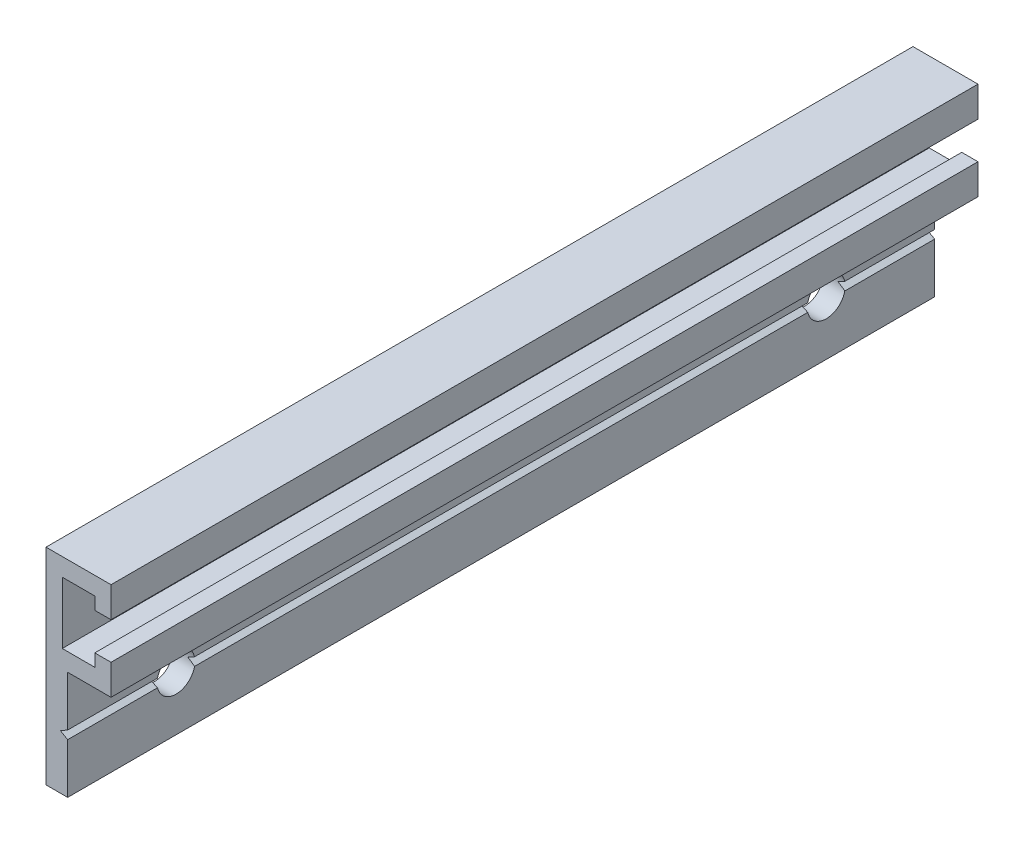
SolidWorks part; units mm, degrees
ref_plane "Front" through (0, 0, 0) normal (0, 0, 1) x (1, 0, 0)
ref_plane "Top" through (0, 0, 0) normal (0, 1, 0) x (1, 0, 0)
ref_plane "Right" through (0, 0, 0) normal (1, 0, 0) x (0, 0, -1)
sketch "Sketch1" plane through (0, 0, 0) normal (0, 0, 1) x (1, 0, 0)
  line L0 (6, -2.8) -> (6, 0)
  line L1 (6, 0) -> (0, 0)
  line L2 (0, 0) -> (0, -19)
  line L3 (0, -19) -> (2, -19)
  line L4 (2, -19) -> (2, -14.3845)
  line L5 (2, -14.3845) -> (1.334, -14)
  line L6 (1.334, -14) -> (2, -13.6155)
  line L7 (2, -13.6155) -> (2, -9)
  line L8 (2, -9) -> (6, -9)
  line L9 (6, -9) -> (6, -6.2)
  line L10 (6, -6.2) -> (4.5, -6.2)
  line L11 (4.5, -6.2) -> (4.5, -7.35)
  line L12 (4.5, -7.35) -> (1.5, -7.35)
  line L13 (1.5, -7.35) -> (1.5, -1.65)
  line L14 (1.5, -1.65) -> (4.5, -1.65)
  line L15 (4.5, -1.65) -> (4.5, -2.8)
  line L16 (4.5, -2.8) -> (6, -2.8)
  line L17 (0.816, -14) -> (2.9153, -14) construction
  line L18 (6.9616, -4.5) -> (-0.9494, -4.5) construction
  dimension "D1" = 19
  dimension "D2" = 3.4
  dimension "D3" = 5.7
  dimension "D4" = 1.5
  dimension "D5" = 3
  dimension "D6" = 1.5
  dimension "D7" = 6
  dimension "D8" = 9
  dimension "D9" = 2
  dimension "D10" = 60
  dimension "D11" = 0.666
  dimension "D13" = 14
  dimension "D14" = 4.5
extrude "Boss-Extrude1" add sketch "Sketch1" against normal blind 80
hole_wizard "Ø3.5 (3.5) Diameter Hole1" positions "Sketch3" profile "Sketch2" hole size "Ø3.5" standard "JIS" end condition through all
sketch "Sketch3" plane through (0, 0, 0) normal (-1, 0, 0) x (0, 0, 1)
  line L0 (0, 0) -> (0, -19) construction
  line L2 (-80, -14) -> (0, -14) construction
  line L3 (-80, -14) -> (0, -14) construction
  point P0 (-10, -14)
  point P1 (-70, -14)
  dimension "D1" = 10
  dimension "D2" = 70
sketch "Sketch2" plane through (0, -14, -10) normal (0, 1, 0) x (0, 0, 1)
  line L0 (0, 0) -> (0, 6)
  line L1 (0, 6) -> (1.75, 6)
  line L2 (1.75, 6) -> (1.75, 0)
  line L5 (1.75, 0) -> (0, 0)
  line L11 (0, -6.35) -> (0, 107.95) construction
  dimension "Thru Hole Dia." = 3.5
  dimension "Thru Hole Depth" = 6
